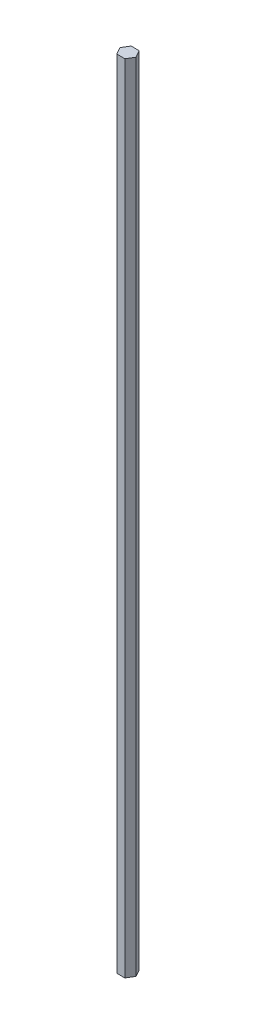
SolidWorks part; units mm, degrees
ref_plane "Front Plane" through (0, 0, 0) normal (0, 0, 1) x (1, 0, 0)
ref_plane "Top Plane" through (0, 0, 0) normal (0, 1, 0) x (1, 0, 0)
ref_plane "Right Plane" through (0, 0, 0) normal (1, 0, 0) x (0, 0, -1)
sketch "Sketch1" plane through (0, 0, 0) normal (0, 1, 0) x (1, 0, 0)
  line L0 (2.7978, -5.2992) -> (6.2668, 0.4868)
  line L1 (6.2668, 0.4868) -> (2.9906, 6.3841)
  line L2 (2.9906, 6.3841) -> (-3.7547, 6.4954)
  line L3 (-3.7547, 6.4954) -> (-7.2238, 0.7094)
  line L4 (-7.2238, 0.7094) -> (-3.9475, -5.1879)
  line L5 (-3.9475, -5.1879) -> (2.7978, -5.2992)
  circle A0 centre (-0.4785, 0.5981) radius 5.8424 construction
extrude "Boss-Extrude1" add sketch "Sketch1" along normal blind 660.4
